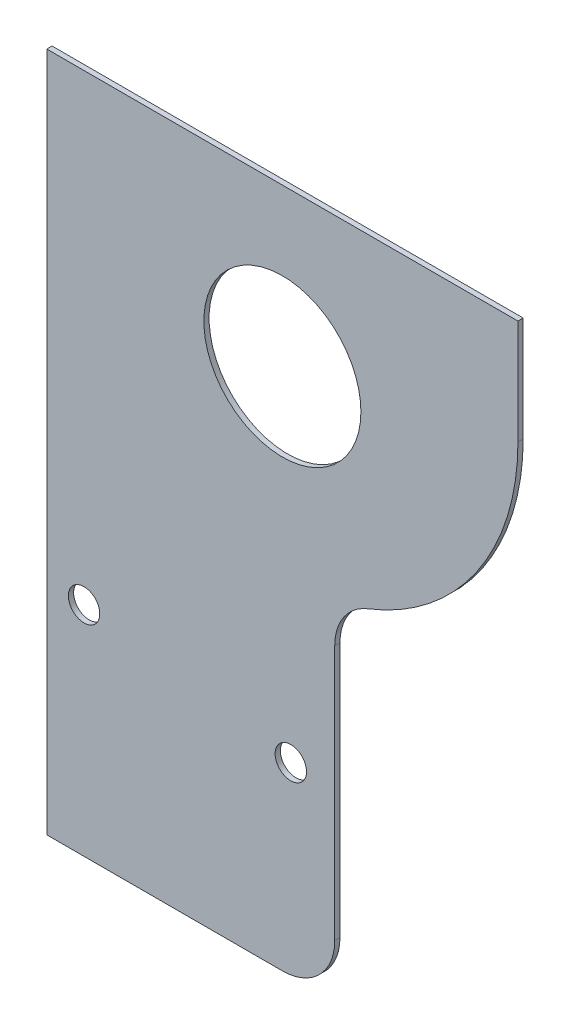
SolidWorks part; units mm, degrees
material "6061 Alloy"
ref_plane "Płaszczyzna XY" through (0, 0, 0) normal (0, 0, 1) x (1, 0, 0)
ref_plane "Płaszczyzna XZ" through (0, 0, 0) normal (0, 1, 0) x (1, 0, 0)
ref_plane "Płaszczyzna YZ" through (0, 0, 0) normal (1, 0, 0) x (0, 0, -1)
ref_plane "Plane1" through (0, 0, 0) normal (0, 0, -1) x (-1, 0, 0)
sketch "Sketch1" plane through (0, 0, 0) normal (0, 0, -1) x (-1, 0, 0)
  line L0 (0, -75) -> (0, 0)
  line L1 (0, 0) -> (-90, 0)
  line L2 (-90, 0) -> (-90, -20)
  line L4 (-55, -71.2348) -> (-55, -120)
  line L5 (-45, -130) -> (0, -130)
  line L6 (0, -130) -> (0, -75)
  circle A0 centre (-45, -30) radius 15
  arc A1 (-90, -20) -> (-61.3636, -61.9193) centre (-45, -20) ccw
  arc A2 (-55, -120) -> (-45, -130) centre (-45, -120) ccw
  arc A3 (-61.3636, -61.9193) -> (-55, -71.2348) centre (-65, -71.2348) cw
  dimension "D1" = 30
  dimension "D2" = 45
  dimension "D3" = 10
  dimension "D4" = 55
  dimension "D5" = 45
  dimension "D6" = 20
  dimension "D7" = 30
  dimension "D8" = 90
  dimension "D9" = 75
  dimension "D11" = 130
extrude "Boss-Extrude1" add sketch "Sketch1" against normal blind 1
sketch "Sketch2" plane through (0, 0, 0) normal (0, 0, -1) x (-1, 0, 0)
  arc A0 (-43.6466, -94.2797) -> (-49.5699, -95.2357) centre (-46.6082, -94.7577) ccw construction
  arc A1 (-49.5699, -95.2357) -> (-43.6466, -94.2797) centre (-46.6082, -94.7577) ccw construction
  arc A2 (-43.6466, -94.2797) -> (-49.5699, -95.2357) centre (-46.6082, -94.7577) ccw
  arc A3 (-49.5699, -95.2357) -> (-43.6466, -94.2797) centre (-46.6082, -94.7577) ccw
  arc A4 (-10.0809, -88.8625) -> (-4.1575, -87.9066) centre (-7.1192, -88.3845) ccw construction
  arc A5 (-4.1575, -87.9066) -> (-10.0809, -88.8625) centre (-7.1192, -88.3845) ccw construction
  arc A6 (-10.0809, -88.8625) -> (-4.1575, -87.9066) centre (-7.1192, -88.3845) ccw
  arc A7 (-4.1575, -87.9066) -> (-10.0809, -88.8625) centre (-7.1192, -88.3845) ccw
extrude "Cut-Extrude1" cut sketch "Sketch2" against normal blind 10
